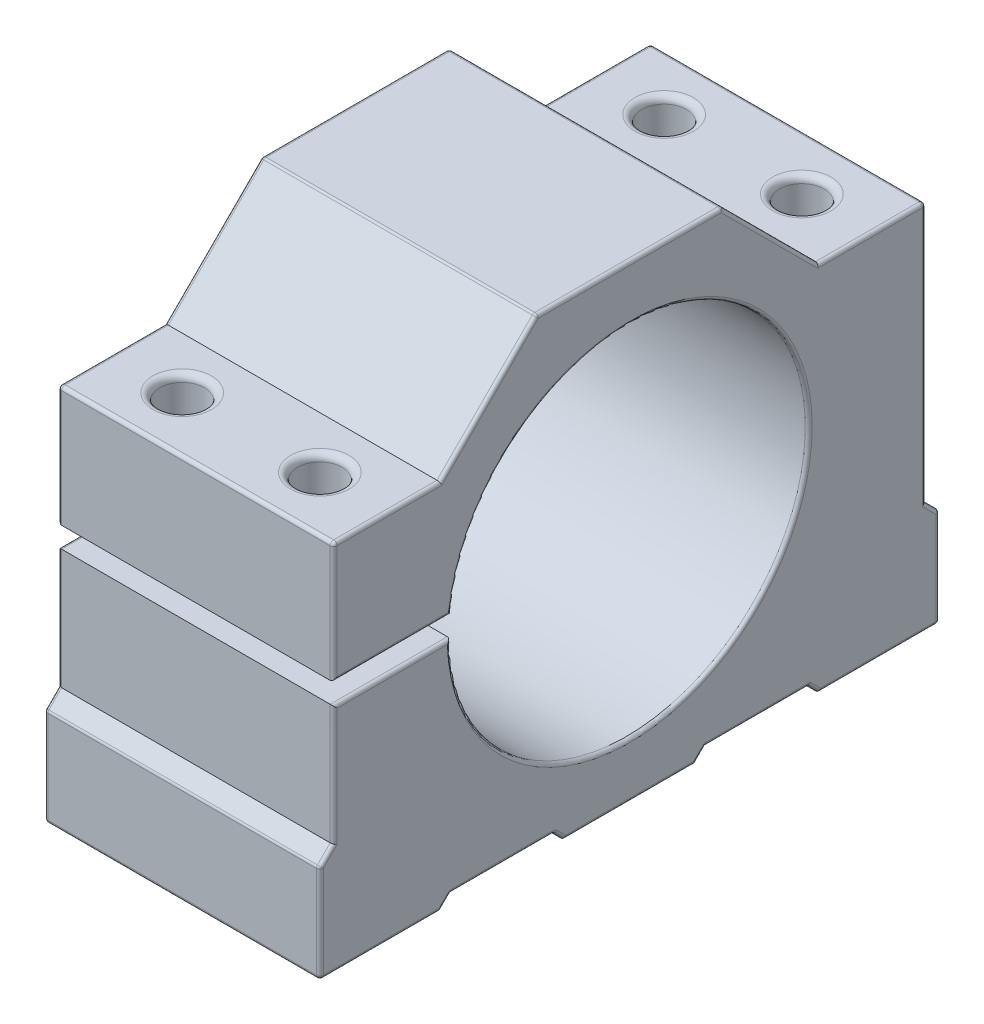
SolidWorks part; units mm, degrees
ref_plane "Спереди" through (0, 0, 0) normal (0, 0, 1) x (1, 0, 0)
ref_plane "Сверху" through (0, 0, 0) normal (0, 1, 0) x (1, 0, 0)
ref_plane "Справа" through (0, 0, 0) normal (1, 0, 0) x (0, 0, -1)
sketch "Эскиз1" plane through (0, 0, 0) normal (1, 0, 0) x (0, 0, -1)
  line L0 (0, 0) -> (90, 0)
  line L1 (0, 0) -> (0, 14.1421)
  line L2 (0, 14.1421) -> (2, 16.1421)
  line L3 (58.5, 68) -> (31.5, 68)
  line L4 (58.5, 68) -> (72.5, 54)
  line L5 (2, 16.1421) -> (2, 54)
  line L6 (2, 54) -> (17.5, 54)
  line L7 (45, 0) -> (45, 68) construction
  line L8 (31.5, 68) -> (17.5, 54)
  line L9 (88, 54) -> (72.5, 54)
  line L10 (88, 16.1421) -> (88, 54)
  line L11 (90, 14.1421) -> (88, 16.1421)
  line L12 (90, 0) -> (90, 14.1421)
  dimension "D1" = 27
  dimension "D2" = 19.799
  dimension "D3" = 135
  dimension "D4" = 14.1421
  dimension "D5" = 16.1421
  dimension "D6" = 54
extrude "Бобышка-Вытянуть1" add sketch "Эскиз1" along normal blind 40
sketch "Эскиз3" plane through (0, 0, 0) normal (-1, 0, 0) x (0, 0, 1)
  line L0 (-45, 68) -> (-45, 0) construction
  line L1 (-58.5, 68) -> (-31.5, 68) construction
  line L2 (0, 0) -> (-90, 0) construction
  line L3 (-2, 54) -> (-2, 16.1421) construction
  line L4 (15.1274, 33.5711) -> (-19.1274, 33.5711)
  line L5 (15.1274, 33.5711) -> (15.1274, 36.5711)
  line L6 (15.1274, 36.5711) -> (-19.1274, 36.5711)
  line L7 (-19.1274, 33.5711) -> (-19.1274, 36.5711)
  line L8 (15.1274, 33.5711) -> (-19.1274, 36.5711) construction
  line L9 (15.1274, 36.5711) -> (-19.1274, 33.5711) construction
  circle A0 centre (-45, 34) radius 26
  point P8 (-2, 35.0711)
  dimension "D1" = 52
extrude "Вырез-Вытянуть1" cut sketch "Эскиз3" against normal blind 40 contours A0 | L4 L7 L6 L5
sketch "Эскиз5" plane through (0, 0, 0) normal (0, -1, 0) x (1, 0, 0)
  line L0 (0, -10) -> (10, -10) construction
  line L1 (0, 0) -> (0, -90) construction
  line L2 (10, 0) -> (10, -10) construction
  line L3 (40, 0) -> (0, 0) construction
  line L4 (0, -45) -> (40, -45) construction
  line L5 (40, 0) -> (40, -90) construction
  circle A0 centre (10, -10) radius 3.25
  circle A1 centre (30, -10) radius 3.25
  circle A2 centre (10, -80) radius 3.25
  circle A3 centre (30, -80) radius 3.25
  dimension "D1" = 6.5
  dimension "D2" = 2
extrude "Вырез-Вытянуть2" cut sketch "Эскиз5" against normal through all
fillet "Скругление1" radius 1 4 edges at (30, 54, -13.25) (10, 54, -13.25) (10, 54, -83.25) (30, 54, -83.25)
sketch "Эскиз6" plane through (0, 0, 0) normal (-1, 0, 0) x (0, 0, 1)
  line L0 (-45, 0) -> (-45, 1.5) construction
  line L2 (0, 0) -> (-90, 0) construction
  line L3 (-34, 1.5) -> (-35.5, 0)
  line L4 (-72.5, 0) -> (-71, 1.5)
  line L5 (-71, 1.5) -> (-56, 1.5)
  line L6 (-56, 1.5) -> (-54.5, 0)
  line L7 (-19, 1.5) -> (-34, 1.5)
  line L8 (-17.5, 0) -> (-19, 1.5)
  line L9 (-72.5, 0) -> (-54.5, 0)
  line L10 (-35.5, 0) -> (-17.5, 0)
  line L11 (-17.5, 0) -> (-17.3773, -0.0674)
  line M18 (-90, 0) -> (0, 0)
extrude "Вырез-Вытянуть3" cut sketch "Эскиз6" against normal blind 40 contours L8 L7 L3 M18 | L5 L6 L9 L4
fillet "Скругление2" radius 0.5 58 edges at (0, 7.0711, -90) (0, 15.1421, -89) (0, 35.0711, -88) (0, 54, -80.25) (0, 61, -65.5) (0, 68, -45) (0, 61, -24.5) (0, 54, -9.75) (0, 45.2855, -2) (0, 36.5711, -10.5637) (0, 32.9271, -70.9779) (0, 33.5711, -10.5018) (0, 24.8566, -2) (0, 15.1421, -1) (0, 7.0711, 0) (0, 0, -8.75) (0, 0.75, -18.25) (0, 1.5, -26.5) (0, 0.75, -34.75) (0, 0, -45) (0, 0.75, -55.25) (0, 1.5, -63.5) (0, 0.75, -71.75) (0, 0, -81.25) (40, 1.5, -63.5) (40, 0.75, -55.25) (40, 0, -45) (40, 0.75, -34.75) (40, 0.75, -18.25) (40, 0, -8.75) (40, 7.0711, 0) (40, 15.1421, -1) (40, 24.8566, -2) (40, 33.5711, -10.5018) (40, 32.9271, -70.9779) (40, 36.5711, -10.5637) (40, 45.2855, -2) (40, 54, -9.75) (40, 61, -24.5) (40, 68, -45) (40, 61, -65.5) (40, 54, -80.25) (40, 35.0711, -88) (40, 15.1421, -89) (40, 7.0711, -90) (40, 0, -81.25) (40, 0.75, -71.75) (20, 1.5, -19) (40, 1.5, -26.5) (20, 1.5, -34) (20, 14.1421, 0) (20, 14.1421, -90) (20, 0, -90) (20, 0, 0) (20, 54, -2) (20, 68, -31.5) (20, 68, -58.5) (20, 54, -88)
